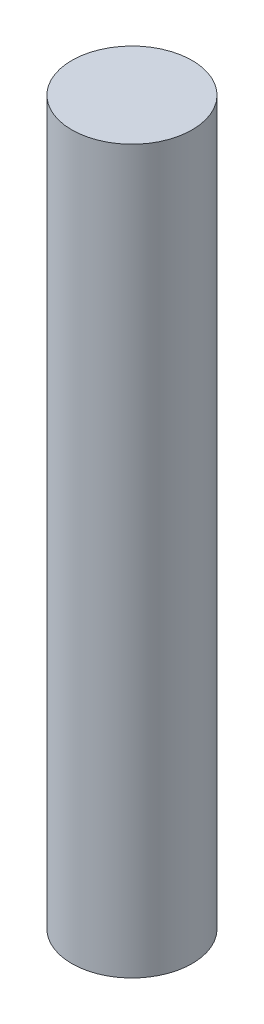
SolidWorks part; units mm, degrees
ref_plane "Front Plane" through (0, 0, 0) normal (0, 0, 1) x (1, 0, 0)
ref_plane "Top Plane" through (0, 0, 0) normal (0, 1, 0) x (1, 0, 0)
ref_plane "Right Plane" through (0, 0, 0) normal (1, 0, 0) x (0, 0, -1)
sketch "Sketch1" plane through (0, 0, 0) normal (0, 1, 0) x (1, 0, 0)
  circle A0 centre (0, 0) radius 2.5
  dimension "D1" = 5
extrude "Boss-Extrude1" add sketch "Sketch1" along normal blind 30
